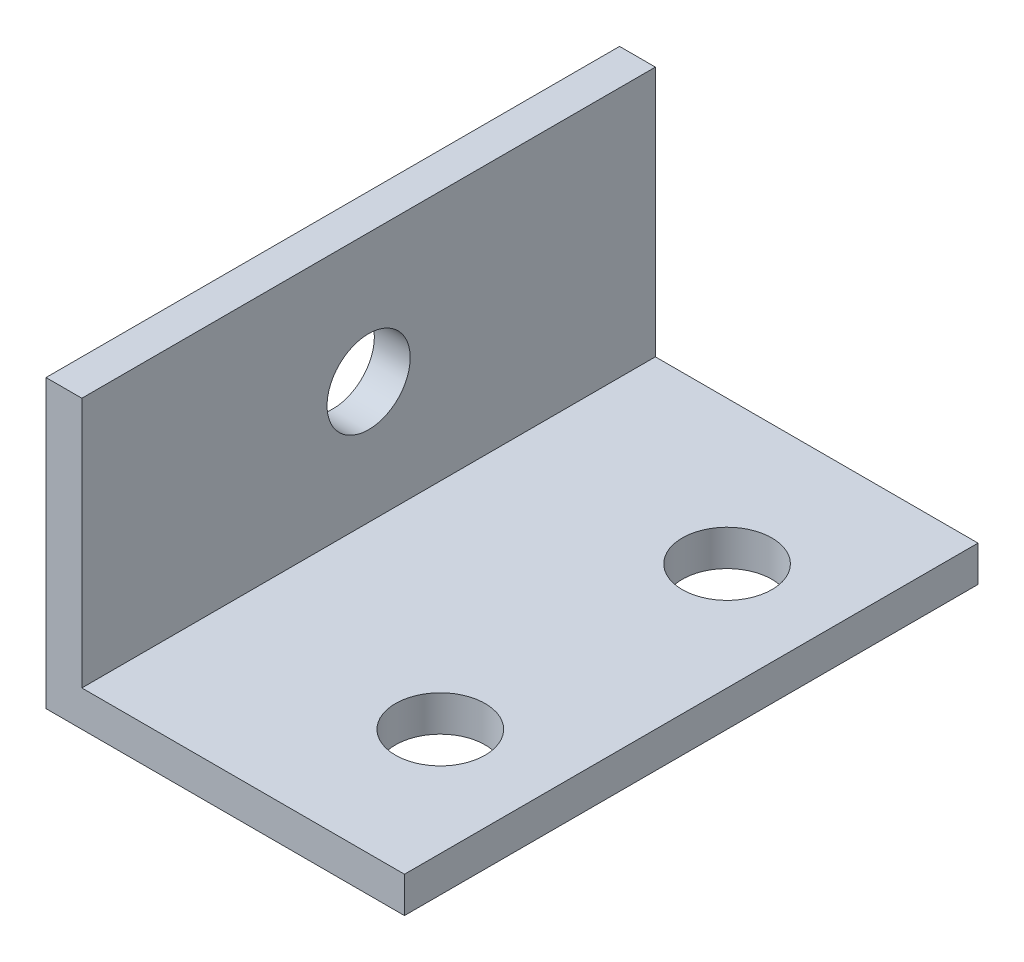
SolidWorks part; units mm, degrees
ref_plane "Front Plane" through (0, 0, 0) normal (0, 0, 1) x (1, 0, 0)
ref_plane "Top Plane" through (0, 0, 0) normal (0, 1, 0) x (1, 0, 0)
ref_plane "Right Plane" through (0, 0, 0) normal (1, 0, 0) x (0, 0, -1)
sketch "Sketch1" plane through (0, 0, 0) normal (0, 0, 1) x (1, 0, 0)
  line L0 (3.175, 3.175) -> (0, 3.175) construction
  line L1 (0, 0) -> (3.175, 0)
  line L2 (0, 0) -> (0, 25.4)
  line L3 (0, 25.4) -> (3.175, 25.4)
  line L4 (3.175, 0) -> (3.175, 25.4)
  line L5 (3.175, 0) -> (31.75, 0)
  line L6 (3.175, 0) -> (3.175, 3.175)
  line L7 (3.175, 3.175) -> (31.75, 3.175)
  line L8 (31.75, 0) -> (31.75, 3.175)
  line L9 (1.5875, 3.175) -> (1.5875, 25.4) construction
  point P11 (1.5875, 14.2875)
  dimension "D1" = 3.175
  dimension "D2" = 3.175
  dimension "D3" = 25.4
  dimension "D4" = 31.75
extrude "Boss-Extrude1" add sketch "Sketch1" along normal blind 50.8 contours L1 L4 L3 L2 | L5 L8 L7 L4
sketch "Sketch2" plane through (3.175, 0, 0) normal (1, 0, 0) x (0, 0, -1)
  line L0 (-50.8, 3.175) -> (-50.8, 25.4) construction
  line L1 (-50.8, 25.4) -> (0, 25.4) construction
  line L2 (0, 25.4) -> (0, 3.175) construction
  line L3 (0, 3.175) -> (-50.8, 3.175) construction
  line L4 (-50.8, 13.97) -> (0, 13.97) construction
  line L5 (-25.4, 25.4) -> (-25.4, 3.175) construction
  circle A0 centre (-25.4, 13.97) radius 3.683
  circle A1 centre (-25.4, 13.97) radius 10.4013 construction
  circle A2 centre (-25.4, 13.97) radius 8.8138 construction
  dimension "D1" = 7.366
  dimension "D2" = 20.8026
  dimension "D3" = 17.6276
  dimension "D4" = 10.795
extrude "Pot Mount" cut sketch "Sketch2" against normal up to next
sketch "Sketch3" plane through (0, 3.175, 0) normal (0, 1, 0) x (1, 0, 0)
  line L0 (3.175, -50.8) -> (31.75, -50.8) construction
  line L1 (31.75, -50.8) -> (31.75, 0) construction
  line L2 (31.75, 0) -> (3.175, 0) construction
  line L3 (3.175, 0) -> (3.175, -50.8) construction
  line L4 (22.225, -50.8) -> (22.225, 0) construction
  circle A0 centre (22.225, -38.1) radius 3.9688
  circle A1 centre (22.225, -12.7) radius 3.9688
  dimension "D2" = 7.9375
  dimension "D3" = 7.9375
  dimension "D1" = 9.525
  dimension "D4" = 25.4
  dimension "D5" = 12.7
extrude "Base Mount" cut sketch "Sketch3" against normal up to next
